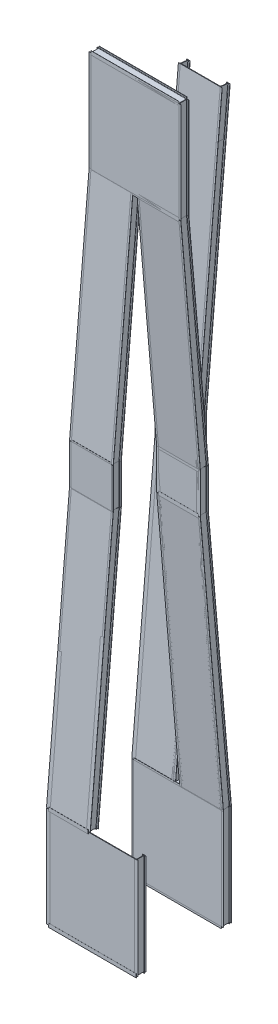
SolidWorks part; units mm, degrees
ref_plane "Plano frontal" through (0, 0, 0) normal (0, 0, 1) x (1, 0, 0)
ref_plane "Plano superior" through (0, 0, 0) normal (0, 1, 0) x (1, 0, 0)
ref_plane "Plano direito" through (0, 0, 0) normal (1, 0, 0) x (0, 0, -1)
sketch3d "3DSketch1"
  line L0 (-19546.6177, 14667.4814, 38871.7002) -> (-19546.6177, -9107.5186, 38871.7002) construction
  line L2 (-19546.6177, -9107.5186, 38871.7002) -> (-19546.6177, -9107.5186, 40471.7002) construction
  line L3 (-19546.6177, -9107.5186, 40471.7002) -> (-19546.6177, 892.4814, 39606.8353)
  line L4 (-19546.6177, 892.4814, 39606.8353) -> (-19546.6177, 2392.4814, 39606.8353)
  line L5 (-19546.6177, 892.4814, 38871.7002) -> (-19546.6177, 892.4814, 39606.8353) construction
  line L6 (-19546.6177, 892.4814, 39606.8353) -> (-19546.6177, 2392.4814, 39606.8353) construction
  line L7 (-19546.6177, 2392.4814, 39606.8353) -> (-19546.6177, 2392.4814, 38871.7002) construction
  line L8 (-19546.6177, 2392.4814, 39606.8353) -> (-19546.6177, 10892.4814, 38871.7002)
  line L9 (-19546.6177, 892.4814, 39606.8353) -> (-19546.6177, -9107.5186, 39606.8353) construction
  line L10 (-19546.6177, -9107.5186, 39606.8353) -> (-18046.6177, -9107.5186, 39606.8353) construction
  line L11 (-18046.6177, -9107.5186, 39606.8353) -> (-18046.6177, 892.4814, 39606.8353) construction
  line L12 (-18046.6177, 892.4814, 39606.8353) -> (-19546.6177, 892.4814, 39606.8353) construction
  line L13 (-18046.6177, 892.4814, 39606.8353) -> (-18046.6177, 2392.4814, 39606.8353) construction
  line L14 (-18046.6177, 2392.4814, 39606.8353) -> (-19546.6177, 2392.4814, 39606.8353) construction
  line L15 (-18046.6177, -9107.5186, 39606.8353) -> (-18046.6177, -9107.5186, 40471.7002) construction
  line L16 (-18046.6177, -9107.5186, 40471.7002) -> (-19546.6177, -9107.5186, 40471.7002) construction
  line L17 (-18046.6177, -9107.5186, 40471.7002) -> (-18046.6177, 892.4814, 39606.8353)
  line L18 (-18046.6177, 892.4814, 39606.8353) -> (-18046.6177, 2392.4814, 39606.8353)
  line L19 (-19546.6177, 10892.4814, 38871.7002) -> (-18046.6177, 10892.4814, 38871.7002) construction
  line L20 (-18046.6177, 10892.4814, 38871.7002) -> (-18046.6177, 2392.4814, 38871.7002) construction
  line L21 (-18046.6177, 2392.4814, 38871.7002) -> (-19546.6177, 2392.4814, 38871.7002) construction
  line L22 (-18046.6177, 2392.4814, 38871.7002) -> (-18046.6177, 2392.4814, 39606.8353) construction
  line L23 (-18046.6177, 2392.4814, 39606.8353) -> (-18046.6177, 10892.4814, 38871.7002)
  line L24 (-18046.6177, 10892.4814, 38871.7002) -> (-19546.6177, 10892.4814, 38871.7002)
  line L25 (-19546.6177, 892.4814, 39606.8353) -> (-18046.6177, 892.4814, 39606.8353)
  line L26 (-19546.6177, 2392.4814, 39606.8353) -> (-18046.6177, 2392.4814, 39606.8353)
  line L27 (-19546.6177, -9107.5186, 40471.7002) -> (-18046.6177, -9107.5186, 40471.7002)
  line L28 (-18046.6177, 2392.4814, 38871.7002) -> (-18046.6177, -9107.5186, 38871.7002) construction
  line L29 (-18046.6177, -9107.5186, 38871.7002) -> (-19546.6177, -9107.5186, 38871.7002) construction
  line L30 (-18046.6177, -9107.5186, 39606.8353) -> (-18046.6177, -9107.5186, 38871.7002) construction
  line L31 (-19546.6177, 14667.4814, 38871.7002) -> (-18046.6177, 14667.4814, 38871.7002) construction
  line L32 (-18046.6177, 14667.4814, 38871.7002) -> (-18046.6177, 10892.4814, 38871.7002) construction
  line L33 (-18046.6177, 892.4814, 39606.8353) -> (-18046.6177, 892.4814, 38871.7002) construction
  line L34 (-18046.6177, -9107.5186, 40471.7002) -> (-17746.6177, -9107.5186, 40471.7002)
  line L35 (-17746.6177, -9107.5186, 40471.7002) -> (-17746.6177, 892.4814, 41336.5651)
  line L36 (-17746.6177, -9107.5186, 40471.7002) -> (-17746.6177, 892.4814, 40471.7002) construction
  line L37 (-17746.6177, 892.4814, 40471.7002) -> (-17746.6177, 892.4814, 41336.5651) construction
  line L38 (-17746.6177, 892.4814, 40471.7002) -> (-16246.6177, 892.4814, 40471.7002) construction
  line L39 (-16246.6177, 892.4814, 40471.7002) -> (-16246.6177, -9107.5186, 40471.7002) construction
  line L40 (-17746.6177, -9107.5186, 40471.7002) -> (-16246.6177, -9107.5186, 40471.7002)
  line L41 (-16246.6177, -9107.5186, 40471.7002) -> (-16246.6177, 892.4814, 41336.5651)
  line L42 (-16246.6177, 892.4814, 41336.5651) -> (-17746.6177, 892.4814, 41336.5651)
  line L43 (-16246.6177, 892.4814, 41336.5651) -> (-16246.6177, 892.4814, 40471.7002) construction
  line L44 (-16246.6177, 892.4814, 40471.7002) -> (-16246.6177, 2392.4814, 40471.7002) construction
  line L45 (-18046.6177, 892.4814, 39606.8353) -> (-18046.6177, 892.4814, 41336.5651) construction
  line L46 (-18046.6177, 892.4814, 41336.5651) -> (-17746.6177, 892.4814, 41336.5651) construction
  line L47 (-16246.6177, 2392.4814, 40471.7002) -> (-17746.6177, 2392.4814, 40471.7002) construction
  line L48 (-17746.6177, 2392.4814, 40471.7002) -> (-17746.6177, 892.4814, 40471.7002) construction
  line L49 (-18046.6177, 2392.4814, 39606.8353) -> (-18046.6177, 2392.4814, 40471.7002) construction
  line L50 (-17746.6177, 2392.4814, 40471.7002) -> (-18046.6177, 2392.4814, 40471.7002) construction
  line L51 (-16246.6177, 2392.4814, 40471.7002) -> (-16246.6177, 2392.4814, 41336.5651) construction
  line L52 (-17746.6177, 2392.4814, 40471.7002) -> (-17746.6177, 2392.4814, 41336.5651) construction
  line L53 (-17746.6177, 892.4814, 41336.5651) -> (-17746.6177, 2392.4814, 41336.5651)
  line L54 (-17746.6177, 2392.4814, 41336.5651) -> (-16246.6177, 2392.4814, 41336.5651)
  line L55 (-16246.6177, 2392.4814, 41336.5651) -> (-16246.6177, 892.4814, 41336.5651)
  line L56 (-16246.6177, 2392.4814, 40471.7002) -> (-16246.6177, 10892.4814, 40471.7002) construction
  line L57 (-16246.6177, 10892.4814, 40471.7002) -> (-17746.6177, 10892.4814, 40471.7002) construction
  line L58 (-17746.6177, 10892.4814, 40471.7002) -> (-17746.6177, 2392.4814, 40471.7002) construction
  line L59 (-16246.6177, 10892.4814, 40471.7002) -> (-16246.6177, 10892.4814, 42071.7002) construction
  line L60 (-16246.6177, 10892.4814, 42071.7002) -> (-17746.6177, 10892.4814, 42071.7002)
  line L61 (-17746.6177, 10892.4814, 42071.7002) -> (-17746.6177, 10892.4814, 40471.7002) construction
  line L62 (-17746.6177, 10892.4814, 40471.7002) -> (-17746.6177, 10892.4814, 38871.7002) construction
  line L63 (-17746.6177, 10892.4814, 38871.7002) -> (-16246.6177, 10892.4814, 38871.7002) construction
  line L64 (-16246.6177, 10892.4814, 38871.7002) -> (-16246.6177, 10892.4814, 40471.7002) construction
  line L65 (-17746.6177, 10892.4814, 38871.7002) -> (-18046.6177, 10892.4814, 38871.7002) construction
  line L66 (-16246.6177, 2392.4814, 41336.5651) -> (-16246.6177, 10892.4814, 42071.7002)
  line L67 (-17746.6177, 10892.4814, 42071.7002) -> (-17746.6177, 2392.4814, 41336.5651)
  line L68 (-18046.6177, 10892.4814, 42071.7002) -> (-18046.6177, -9107.5186, 42071.7002) construction
  line L69 (-17746.6177, 10892.4814, 42071.7002) -> (-18046.6177, 10892.4814, 42071.7002)
  line L70 (-18046.6177, 2392.4814, 40471.7002) -> (-18046.6177, 2392.4814, 41336.5651) construction
  line L71 (-18046.6177, 2392.4814, 41336.5651) -> (-17746.6177, 2392.4814, 41336.5651) construction
  line L72 (-18046.6177, 2392.4814, 41336.5651) -> (-18046.6177, 2392.4814, 42806.8353) construction
  line L73 (-18046.6177, 10892.4814, 42071.7002) -> (-18046.6177, 2392.4814, 42806.8353)
  line L74 (-18046.6177, 2392.4814, 42806.8353) -> (-18046.6177, 892.4814, 42806.8353)
  line L75 (-18046.6177, 892.4814, 42806.8353) -> (-18046.6177, -9107.5186, 43671.7002)
  line L76 (-18046.6177, -9107.5186, 40471.7002) -> (-18046.6177, -9107.5186, 42071.7002) construction
  line L77 (-18046.6177, 892.4814, 41336.5651) -> (-18046.6177, 892.4814, 42806.8353) construction
  line L78 (-18046.6177, -9107.5186, 43671.7002) -> (-18046.6177, -9107.5186, 42071.7002)
  line L79 (-19546.6177, -9107.5186, 40471.7002) -> (-19546.6177, -9107.5186, 42071.7002) construction
  line L80 (-19546.6177, -9107.5186, 42071.7002) -> (-18046.6177, -9107.5186, 42071.7002) construction
  line L81 (-19546.6177, -9107.5186, 42071.7002) -> (-19546.6177, 10892.4814, 42071.7002) construction
  line L82 (-18046.6177, 10892.4814, 42071.7002) -> (-19546.6177, 10892.4814, 42071.7002) construction
  line L83 (-18046.6177, 892.4814, 42806.8353) -> (-19546.6177, 892.4814, 42806.8353) construction
  line L84 (-19546.6177, 892.4814, 42806.8353) -> (-19546.6177, 2392.4814, 42806.8353) construction
  line L85 (-19546.6177, 2392.4814, 42806.8353) -> (-18046.6177, 2392.4814, 42806.8353) construction
  line L86 (-19546.6177, -9107.5186, 42071.7002) -> (-19546.6177, -9107.5186, 42806.8353) construction
  line L87 (-19546.6177, -9107.5186, 42806.8353) -> (-19546.6177, 892.4814, 42806.8353) construction
  line L88 (-19546.6177, -9107.5186, 42071.7002) -> (-19546.6177, -9107.5186, 43671.7002)
  line L89 (-19546.6177, -9107.5186, 43671.7002) -> (-18046.6177, -9107.5186, 43671.7002)
  line L90 (-19546.6177, -9107.5186, 43671.7002) -> (-19546.6177, 892.4814, 42806.8353)
  line L91 (-19546.6177, 892.4814, 42806.8353) -> (-19546.6177, 2392.4814, 42806.8353)
  line L92 (-19546.6177, 2392.4814, 42806.8353) -> (-19546.6177, 10892.4814, 42071.7002)
  line L93 (-19546.6177, 10892.4814, 42071.7002) -> (-18046.6177, 10892.4814, 42071.7002)
  line L94 (-19546.6177, 14667.4814, 42071.7002) -> (-19546.6177, 14667.4814, 38871.7002) construction
  line L95 (-19546.6177, 10892.4814, 42071.7002) -> (-16246.6177, 10892.4814, 42071.7002)
  line L96 (-19546.6177, 10892.4814, 42071.7002) -> (-19546.6177, 14667.4814, 42071.7002)
  line L97 (-19546.6177, 14667.4814, 42071.7002) -> (-16246.6177, 14667.4814, 42071.7002)
  line L98 (-16246.6177, 10892.4814, 42071.7002) -> (-16246.6177, 14667.4814, 42071.7002)
  line L99 (-18046.6177, 2392.4814, 42806.8353) -> (-19546.6177, 2392.4814, 42806.8353)
  line L100 (-18046.6177, 892.4814, 42806.8353) -> (-19546.6177, 892.4814, 42806.8353)
  line L101 (-19546.6177, 14667.4814, 42071.7002) -> (-19546.6177, 14667.4814, 38871.7002)
  line L102 (-16246.6177, 14667.4814, 42071.7002) -> (-16246.6177, 14667.4814, 38871.7002)
  line L103 (-18046.6177, 14667.4814, 38871.7002) -> (-16246.6177, 14667.4814, 38871.7002) construction
  line L104 (-18046.6177, -9107.5186, 42071.7002) -> (-18046.6177, -9107.5186, 38871.7002)
  line L105 (-19546.6177, -9107.5186, 42071.7002) -> (-19546.6177, -9107.5186, 38871.7002)
  line L106 (-18046.6177, -9107.5186, 38871.7002) -> (-16246.6177, -9107.5186, 38871.7002) construction
  line L107 (-16246.6177, -9107.5186, 40471.7002) -> (-16246.6177, -9107.5186, 38871.7002)
  line L108 (-18046.6177, 892.4814, 39606.8353) -> (-18046.6177, 892.4814, 38871.7002)
  line L109 (-18046.6177, 2392.4814, 39606.8353) -> (-18046.6177, 2392.4814, 38871.7002)
  line L110 (-19546.6177, 892.4814, 39606.8353) -> (-19546.6177, 892.4814, 38871.7002)
  line L111 (-19546.6177, 2392.4814, 39606.8353) -> (-19546.6177, 2392.4814, 38871.7002)
  line L112 (-18046.6177, 892.4814, 38871.7002) -> (-16246.6177, 892.4814, 38871.7002) construction
  line L113 (-18046.6177, 2392.4814, 38871.7002) -> (-16246.6177, 2392.4814, 38871.7002) construction
  line L114 (-16246.6177, 892.4814, 41336.5651) -> (-16246.6177, 892.4814, 38871.7002)
  line L115 (-16246.6177, 2392.4814, 41336.5651) -> (-16246.6177, 2392.4814, 38871.7002)
  line L116 (-17746.6177, 892.4814, 41336.5651) -> (-17746.6177, 892.4814, 38871.7002)
  line L117 (-17746.6177, 2392.4814, 41336.5651) -> (-17746.6177, 2392.4814, 38871.7002)
  line L118 (-18046.6177, 892.4814, 42806.8353) -> (-18046.6177, 892.4814, 38871.7002)
  line L119 (-18046.6177, 2392.4814, 42806.8353) -> (-18046.6177, 2392.4814, 38871.7002)
  line L120 (-19546.6177, 892.4814, 42806.8353) -> (-19546.6177, 892.4814, 38871.7002)
  line L121 (-19546.6177, 2392.4814, 42806.8353) -> (-19546.6177, 2392.4814, 38871.7002)
  line L122 (-18046.6177, 14667.4814, 38871.7002) -> (-18046.6177, 14667.4814, 42071.7002)
  line L123 (-19546.6177, -12882.5186, 40471.7002) -> (-19546.6177, -12882.5186, 43671.7002) construction
  line L124 (-16246.6177, 892.4814, 41336.5651) -> (-17746.6177, 892.4814, 41336.5651)
  line L125 (-16246.6177, 892.4814, 41336.5651) -> (-16246.6177, 2392.4814, 41336.5651)
  line L126 (-16246.6177, 2392.4814, 41336.5651) -> (-17746.6177, 2392.4814, 41336.5651)
  line L127 (-17746.6177, 892.4814, 41336.5651) -> (-17746.6177, 2392.4814, 41336.5651)
  line L128 (-16246.6177, 892.4814, 41336.5651) -> (-17746.6177, 892.4814, 41336.5651)
  line L129 (-16246.6177, 892.4814, 41336.5651) -> (-16246.6177, -9107.5186, 40471.7002)
  line L130 (-16246.6177, -9107.5186, 40471.7002) -> (-17746.6177, -9107.5186, 40471.7002)
  line L131 (-17746.6177, 892.4814, 41336.5651) -> (-17746.6177, -9107.5186, 40471.7002)
  line L132 (-19546.6177, 2392.4814, 42806.8353) -> (-18046.6177, 2392.4814, 42806.8353)
  line L133 (-19546.6177, 2392.4814, 42806.8353) -> (-19546.6177, 10892.4814, 42071.7002)
  line L134 (-19546.6177, 10892.4814, 42071.7002) -> (-18046.6177, 10892.4814, 42071.7002)
  line L135 (-18046.6177, 2392.4814, 42806.8353) -> (-18046.6177, 10892.4814, 42071.7002)
  line L136 (-19546.6177, 892.4814, 42806.8353) -> (-18046.6422, 892.4569, 42806.5528)
  line L137 (-19546.6177, 892.4814, 42806.8353) -> (-19546.5932, 2392.5058, 42807.1179)
  line L138 (-19546.5932, 2392.5058, 42807.1179) -> (-18046.6177, 2392.4814, 42806.8353)
  line L139 (-18046.6422, 892.4569, 42806.5528) -> (-18046.6177, 2392.4814, 42806.8353)
  line L140 (-19546.6177, -9107.5186, 43671.7002) -> (-18046.6422, -9107.5431, 43671.4176)
  line L141 (-19546.6177, -9107.5186, 43671.7002) -> (-19546.6177, 892.4814, 42806.8353)
  line L142 (-19546.6177, 892.4814, 42806.8353) -> (-18046.6422, 892.4569, 42806.5528)
  line L143 (-18046.6422, -9107.5431, 43671.4176) -> (-18046.6422, 892.4569, 42806.5528)
  line L144 (-19546.6177, -9107.5186, 40471.7002) -> (-18046.6177, -9107.5186, 40471.7002)
  line L145 (-19546.6177, -9107.5186, 40471.7002) -> (-19546.6177, 892.4814, 39606.8353)
  line L146 (-19546.6177, 892.4814, 39606.8353) -> (-18046.6177, 892.4814, 39606.8353)
  line L147 (-18046.6177, -9107.5186, 40471.7002) -> (-18046.6177, 892.4814, 39606.8353)
  line L148 (-19546.6177, 2392.4814, 39606.8353) -> (-18046.6177, 2392.4814, 39606.8353)
  line L149 (-19546.6177, 2392.4814, 39606.8353) -> (-19546.6177, 892.4814, 39606.8353)
  line L150 (-19546.6177, 892.4814, 39606.8353) -> (-18046.6177, 892.4814, 39606.8353)
  line L151 (-18046.6177, 2392.4814, 39606.8353) -> (-18046.6177, 892.4814, 39606.8353)
  line L152 (-19546.6177, 10892.4814, 38871.7002) -> (-18046.6177, 10892.4814, 38871.7002)
  line L153 (-19546.6177, 10892.4814, 38871.7002) -> (-19546.6177, 2392.4814, 39606.8353)
  line L154 (-19546.6177, 2392.4814, 39606.8353) -> (-18046.6177, 2392.4814, 39606.8353)
  line L155 (-18046.6177, 10892.4814, 38871.7002) -> (-18046.6177, 2392.4814, 39606.8353)
  line L156 (-19546.6177, -9107.5186, 40471.7002) -> (-16246.6177, -9107.5186, 40471.7002)
  line L157 (-19546.6177, -9107.5186, 40471.7002) -> (-19546.6177, -12882.5186, 40471.7002)
  line L158 (-19546.6177, -12882.5186, 40471.7002) -> (-16246.6177, -12882.5186, 40471.7002)
  line L159 (-16246.6177, -9107.5186, 40471.7002) -> (-16246.6177, -12882.5186, 40471.7002)
  line L160 (-19546.6177, -12882.5186, 43671.7002) -> (-19546.6177, -9107.5186, 43671.7002) construction
  line L161 (-18046.6177, 10892.4814, 38871.7002) -> (-18046.6177, 13532.0913, 38871.7002) construction
  line L162 (-19546.6177, -9107.5186, 43671.7002) -> (-16246.6177, -9107.5186, 43671.7002)
  line L163 (-19546.6177, -9107.5186, 43671.7002) -> (-19546.6177, -12882.5186, 43671.7002)
  line L164 (-19546.6177, -12882.5186, 43671.7002) -> (-16246.6177, -12882.5186, 43671.7002)
  line L165 (-16246.6177, -9107.5186, 43671.7002) -> (-16246.6177, -12882.5186, 43671.7002)
  line L166 (-18046.6177, 10892.4814, 38871.7002) -> (-19546.6177, 10892.4814, 38871.7002)
  line L167 (-18046.6177, 10892.4814, 38871.7002) -> (-18046.6177, 12626.8564, 38721.7002)
  line L168 (-18046.6177, 12626.8564, 38721.7002) -> (-19546.6177, 12626.8564, 38721.7002)
  line L169 (-19546.6177, 10892.4814, 38871.7002) -> (-19546.6177, 12626.8564, 38721.7002)
  line L170 (-18046.6177, 12626.8564, 38871.7002) -> (-18046.6177, 12626.8564, 38721.7002) construction
  line L172 (-19546.6177, -9082.5186, 41771.7002) -> (-19546.6177, -9082.5186, 38871.7002) construction
  dimension "D1" = 10000
  dimension "D3" = 8500
  dimension "D2" = 1600
  dimension "D6" = 300
  dimension "D4" = 1500
  dimension "D5" = 1500
  dimension "D7" = 150
  dimension "D8" = 25
other "Al i beam standard AL I BEAM STD 12X17.3(1)"
ref_plane "Plane1" through (-18046.6177, 2392.4814, 39606.8353) normal (0, 0.9963, -0.0862) x (1, 0, 0)
sketch "Sketch1" plane through (-18046.6177, 2392.4814, 39606.8353) normal (0, 0.9963, -0.0862) x (1, 0, 0)
  line L0 (-69.596, -151.2794) -> (-69.596, -149.8037)
  line L1 (-63.2891, -142.7374) -> (-21.3386, -137.9576)
  line L2 (-8.7249, -123.825) -> (-8.7249, 123.825)
  line L3 (-20.6103, 137.8554) -> (-63.6533, 145.0298)
  line L4 (-69.596, 152.045) -> (-69.596, 153.5206)
  line L5 (-69.596, 153.5206) -> (69.596, 153.5206)
  line L6 (69.596, 153.5206) -> (69.596, 152.045)
  line L7 (63.6533, 145.0298) -> (20.6103, 137.8554)
  line L8 (8.7249, 123.825) -> (8.7249, -123.825)
  line L9 (21.3386, -137.9576) -> (63.2891, -142.7374)
  line L10 (69.596, -149.8037) -> (69.596, -151.2794)
  line L11 (69.596, -151.2794) -> (-69.596, -151.2794)
  line L14 (-8.7249, 0) -> (8.7249, 0) construction
  arc A0 (-21.3386, -137.9576) -> (-8.7249, -123.825) centre (-22.9489, -123.825) ccw
  arc A1 (-8.7249, 123.825) -> (-20.6103, 137.8554) centre (-22.9489, 123.825) ccw
  arc A2 (20.6103, 137.8554) -> (8.7249, 123.825) centre (22.9489, 123.825) ccw
  arc A3 (8.7249, -123.825) -> (21.3386, -137.9576) centre (22.9489, -123.825) ccw
  arc A4 (63.6533, 145.0298) -> (69.596, 152.045) centre (62.484, 152.045) ccw
  arc A5 (-63.6533, 145.0298) -> (-69.596, 152.045) centre (-62.484, 152.045) cw
  arc A6 (63.2891, -142.7374) -> (69.596, -149.8037) centre (62.484, -149.8037) cw
  arc A7 (-63.2891, -142.7374) -> (-69.596, -149.8037) centre (-62.484, -149.8037) ccw
  point P30 (0, 153.5206)
  point P31 (0, -151.2794)
  point P33 (0, 0)
  point P34 (0, 0)
  dimension "D7" = 6.5
  dimension "RI" = 14.224
  dimension "RA" = 7.112
  dimension "BF" = 139.192
  dimension "D6" = 9.463
  dimension "DEPTH" = 304.8
  dimension "TW" = 17.4498
  dimension "D1" = 247.65
other "Al i beam standard AL I BEAM STD 12X17.3(2)"
ref_plane "Plane2" through (-18046.6177, 892.4814, 39606.8353) normal (0, 1, 0) x (1, 0, 0)
sketch "Sketch11" plane through (-18046.6177, 892.4814, 39606.8353) normal (0, 1, 0) x (1, 0, 0)
  line L0 (-69.596, -151.2794) -> (-69.596, -149.8037)
  line L1 (-63.2891, -142.7374) -> (-21.3386, -137.9576)
  line L2 (-8.7249, -123.825) -> (-8.7249, 123.825)
  line L3 (-20.6103, 137.8554) -> (-63.6533, 145.0298)
  line L4 (-69.596, 152.045) -> (-69.596, 153.5206)
  line L5 (-69.596, 153.5206) -> (69.596, 153.5206)
  line L6 (69.596, 153.5206) -> (69.596, 152.045)
  line L7 (63.6533, 145.0298) -> (20.6103, 137.8554)
  line L8 (8.7249, 123.825) -> (8.7249, -123.825)
  line L9 (21.3386, -137.9576) -> (63.2891, -142.7374)
  line L10 (69.596, -149.8037) -> (69.596, -151.2794)
  line L11 (69.596, -151.2794) -> (-69.596, -151.2794)
  line L14 (-8.7249, 0) -> (8.7249, 0) construction
  arc A0 (-21.3386, -137.9576) -> (-8.7249, -123.825) centre (-22.9489, -123.825) ccw
  arc A1 (-8.7249, 123.825) -> (-20.6103, 137.8554) centre (-22.9489, 123.825) ccw
  arc A2 (20.6103, 137.8554) -> (8.7249, 123.825) centre (22.9489, 123.825) ccw
  arc A3 (8.7249, -123.825) -> (21.3386, -137.9576) centre (22.9489, -123.825) ccw
  arc A4 (63.6533, 145.0298) -> (69.596, 152.045) centre (62.484, 152.045) ccw
  arc A5 (-63.6533, 145.0298) -> (-69.596, 152.045) centre (-62.484, 152.045) cw
  arc A6 (63.2891, -142.7374) -> (69.596, -149.8037) centre (62.484, -149.8037) cw
  arc A7 (-63.2891, -142.7374) -> (-69.596, -149.8037) centre (-62.484, -149.8037) ccw
  point P30 (0, 153.5206)
  point P31 (0, -151.2794)
  point P33 (0, 0)
  point P34 (0, 0)
  dimension "D7" = 6.5
  dimension "RI" = 14.224
  dimension "RA" = 7.112
  dimension "BF" = 139.192
  dimension "D6" = 9.463
  dimension "DEPTH" = 304.8
  dimension "TW" = 17.4498
  dimension "D1" = 247.65
other "Al i beam standard AL I BEAM STD 12X17.3(3)"
ref_plane "Plane3" through (-19546.6177, -9107.5186, 40471.7002) normal (1, 0, 0) x (0, 0, -1)
sketch "Sketch12" plane through (-19546.6177, -9107.5186, 40471.7002) normal (1, 0, 0) x (0, 0, -1)
  line L0 (151.2794, -69.596) -> (149.8037, -69.596)
  line L1 (142.7374, -63.2891) -> (137.9576, -21.3386)
  line L2 (123.825, -8.7249) -> (-123.825, -8.7249)
  line L3 (-137.8554, -20.6103) -> (-145.0298, -63.6533)
  line L4 (-152.045, -69.596) -> (-153.5206, -69.596)
  line L5 (-153.5206, -69.596) -> (-153.5206, 69.596)
  line L6 (-153.5206, 69.596) -> (-152.045, 69.596)
  line L7 (-145.0298, 63.6533) -> (-137.8554, 20.6103)
  line L8 (-123.825, 8.7249) -> (123.825, 8.7249)
  line L9 (137.9576, 21.3386) -> (142.7374, 63.2891)
  line L10 (149.8037, 69.596) -> (151.2794, 69.596)
  line L11 (151.2794, 69.596) -> (151.2794, -69.596)
  line L14 (0, -8.7249) -> (0, 8.7249) construction
  arc A0 (137.9576, -21.3386) -> (123.825, -8.7249) centre (123.825, -22.9489) ccw
  arc A1 (-123.825, -8.7249) -> (-137.8554, -20.6103) centre (-123.825, -22.9489) ccw
  arc A2 (-137.8554, 20.6103) -> (-123.825, 8.7249) centre (-123.825, 22.9489) ccw
  arc A3 (123.825, 8.7249) -> (137.9576, 21.3386) centre (123.825, 22.9489) ccw
  arc A4 (-145.0298, 63.6533) -> (-152.045, 69.596) centre (-152.045, 62.484) ccw
  arc A5 (-145.0298, -63.6533) -> (-152.045, -69.596) centre (-152.045, -62.484) cw
  arc A6 (142.7374, 63.2891) -> (149.8037, 69.596) centre (149.8037, 62.484) cw
  arc A7 (142.7374, -63.2891) -> (149.8037, -69.596) centre (149.8037, -62.484) ccw
  point P30 (-153.5206, 0)
  point P31 (151.2794, 0)
  point P33 (0, 0)
  point P34 (0, 0)
  dimension "D7" = 6.5
  dimension "RI" = 14.224
  dimension "RA" = 7.112
  dimension "BF" = 139.192
  dimension "D6" = 9.463
  dimension "DEPTH" = 304.8
  dimension "TW" = 17.4498
  dimension "D1" = 247.65
other "Al i beam standard AL I BEAM STD 12X17.3(12)"
ref_plane "Plane4" through (-16246.6177, -9107.5186, 40471.7002) normal (0, 0.9963, 0.0862) x (1, 0, 0)
sketch "Sketch13" plane through (-16246.6177, -9107.5186, 40471.7002) normal (0, 0.9963, 0.0862) x (1, 0, 0)
  line L0 (-69.596, -151.2794) -> (-69.596, -149.8037)
  line L1 (-63.2891, -142.7374) -> (-21.3386, -137.9576)
  line L2 (-8.7249, -123.825) -> (-8.7249, 123.825)
  line L3 (-20.6103, 137.8554) -> (-63.6533, 145.0298)
  line L4 (-69.596, 152.045) -> (-69.596, 153.5206)
  line L5 (-69.596, 153.5206) -> (69.596, 153.5206)
  line L6 (69.596, 153.5206) -> (69.596, 152.045)
  line L7 (63.6533, 145.0298) -> (20.6103, 137.8554)
  line L8 (8.7249, 123.825) -> (8.7249, -123.825)
  line L9 (21.3386, -137.9576) -> (63.2891, -142.7374)
  line L10 (69.596, -149.8037) -> (69.596, -151.2794)
  line L11 (69.596, -151.2794) -> (-69.596, -151.2794)
  line L14 (-8.7249, 0) -> (8.7249, 0) construction
  arc A0 (-21.3386, -137.9576) -> (-8.7249, -123.825) centre (-22.9489, -123.825) ccw
  arc A1 (-8.7249, 123.825) -> (-20.6103, 137.8554) centre (-22.9489, 123.825) ccw
  arc A2 (20.6103, 137.8554) -> (8.7249, 123.825) centre (22.9489, 123.825) ccw
  arc A3 (8.7249, -123.825) -> (21.3386, -137.9576) centre (22.9489, -123.825) ccw
  arc A4 (63.6533, 145.0298) -> (69.596, 152.045) centre (62.484, 152.045) ccw
  arc A5 (-63.6533, 145.0298) -> (-69.596, 152.045) centre (-62.484, 152.045) cw
  arc A6 (63.2891, -142.7374) -> (69.596, -149.8037) centre (62.484, -149.8037) cw
  arc A7 (-63.2891, -142.7374) -> (-69.596, -149.8037) centre (-62.484, -149.8037) ccw
  point P30 (0, 153.5206)
  point P31 (0, -151.2794)
  point P33 (0, 0)
  point P34 (0, 0)
  dimension "D7" = 6.5
  dimension "RI" = 14.224
  dimension "RA" = 7.112
  dimension "BF" = 139.192
  dimension "D6" = 9.463
  dimension "DEPTH" = 304.8
  dimension "TW" = 17.4498
  dimension "D1" = 247.65
sketch "Sketch14" plane through (0, 3430.8218, 39668.877) normal (0, 0.0862, 0.9963) x (1, 0, 0)
  line L0 (-19477.0217, -2523.5543) -> (-19477.0217, -12560.8841) construction
  line L1 (-19477.0217, -2523.5543) -> (-18046.6177, -2523.5543)
  line L2 (-19477.0217, -2523.5543) -> (-19477.0217, -12504.7751)
  line L3 (-19477.0217, -12504.7751) -> (-18046.6177, -12504.7751)
  line L4 (-18046.6177, -2523.5543) -> (-18046.6177, -12504.7751)
  line L5 (-18046.6177, -12504.7751) -> (-19546.6177, -12504.7751) construction
  line L6 (-18046.6177, -12560.8841) -> (-18046.6177, -2523.5543) construction
  line L7 (-19546.6177, -2523.5543) -> (-18046.6177, -2523.5543) construction
extrude "Boss-Extrude5" add sketch "Sketch14" against normal blind 20 from surface at -129.2473 separate body starting at face at (-18046.6177, -4094.4837, 40189.9845)
sketch "Sketch15" plane through (0, 0, 40625.2208) normal (0, 0, 1) x (1, 0, 0)
  line L1 (-19546.6177, -9107.5186) -> (-16246.6177, -9107.5186)
  line L2 (-19546.6177, -9107.5186) -> (-19546.6177, -12882.5186)
  line L3 (-19546.6177, -12882.5186) -> (-16246.6177, -12882.5186)
  line L4 (-16246.6177, -9107.5186) -> (-16246.6177, -12882.5186)
extrude "Boss-Extrude6" add sketch "Sketch15" against normal blind 20 from surface at 0 separate body starting at face at (-18796.6177, -9107.5186, 40625.2208)
sketch "Sketch16" plane through (0, -3554.9206, 41103.769) normal (0, -0.0862, 0.9963) x (1, 0, 0)
  line L1 (-17746.6177, 4450.9204) -> (-16246.6177, 4450.9204)
  line L2 (-17746.6177, 4450.9204) -> (-17746.6177, -5573.1814)
  line L3 (-17746.6177, -5573.1814) -> (-16246.6177, -5573.1814)
  line L4 (-16246.6177, 4450.9204) -> (-16246.6177, -5573.1814)
extrude "Boss-Extrude7" add sketch "Sketch16" against normal blind 20 from surface at 0 separate body starting at face at (-16246.6177, -4120.5536, 41054.8494)
sketch "Sketch17" plane through (0, 0, 43822.9795) normal (0, 0, 1) x (1, 0, 0)
  line L1 (-19546.6177, -9107.5186) -> (-16246.6177, -9107.5186)
  line L2 (-19546.6177, -9107.5186) -> (-19546.6177, -12882.5186)
  line L3 (-19546.6177, -12882.5186) -> (-16246.6177, -12882.5186)
  line L4 (-16246.6177, -9107.5186) -> (-16246.6177, -12882.5186)
extrude "Boss-Extrude8" add sketch "Sketch17" against normal blind 20 from surface at 0 separate body starting at face at (-19546.6177, -10995.0186, 43822.9795)
sketch "Sketch18" plane through (0, 3694.3872, 42716.3524) normal (0, 0.0862, 0.9963) x (1, 0, 0)
  line L1 (-18046.6177, -12836.6116) -> (-19546.6177, -12836.6116)
  line L2 (-18046.6177, -12836.6116) -> (-18046.6177, -2799.2817)
  line L3 (-18046.6177, -2799.2817) -> (-19546.6177, -2799.2817)
  line L4 (-19546.6177, -12836.6116) -> (-19546.6177, -2799.2817)
extrude "Boss-Extrude9" add sketch "Sketch18" against normal blind 20 from surface at 0 separate body starting at face at (-19546.6177, -4094.4837, 43389.9845)
sketch "Sketch19" plane through (0, 0, 42960.356) normal (0, 0, 1) x (1, 0, 0)
  line L1 (-19555.3426, 2403.1507) -> (-18046.6177, 2403.1507)
  line L2 (-19555.3426, 2403.1507) -> (-19555.3426, 892.4814)
  line L3 (-19555.3426, 892.4814) -> (-18046.6177, 892.4814)
  line L4 (-18046.6177, 2403.1507) -> (-18046.6177, 892.4814)
extrude "Boss-Extrude10" add sketch "Sketch19" against normal blind 20 from surface at 0 separate body starting at face at (-18796.6177, 2392.4814, 42960.356)
sketch "Sketch20" plane through (0, 3705.5238, 42845.119) normal (0, 0.0862, 0.9963) x (1, 0, 0)
  line L1 (-18046.6177, -1306.8902) -> (-19546.6177, -1306.8902)
  line L2 (-18046.6177, -1306.8902) -> (-18046.6177, 7226.87)
  line L3 (-18046.6177, 7226.87) -> (-19546.6177, 7226.87)
  line L4 (-19546.6177, -1306.8902) -> (-19546.6177, 7226.87)
extrude "Boss-Extrude11" add sketch "Sketch20" against normal blind 20 from surface at 0 separate body starting at face at (-19546.6177, 6655.5163, 42589.9845)
sketch "Sketch21" plane through (0, 0, 42225.2208) normal (0, 0, 1) x (1, 0, 0)
  line L1 (-19546.6177, 14667.4814) -> (-16237.8928, 14667.4814)
  line L2 (-19546.6177, 14667.4814) -> (-19546.6177, 10881.812)
  line L3 (-19546.6177, 10881.812) -> (-16237.8928, 10881.812)
  line L4 (-16237.8928, 14667.4814) -> (-16237.8928, 10881.812)
extrude "Boss-Extrude12" add sketch "Sketch21" against normal blind 20 from surface at 0 separate body starting at face at (-17896.6177, 14667.4814, 42225.2208)
sketch "Sketch22" plane through (0, -3543.784, 40975.0024) normal (0, -0.0862, 0.9963) x (1, 0, 0)
  line L1 (-17746.6177, 14477.0722) -> (-16246.6177, 14477.0722)
  line L2 (-17746.6177, 14477.0722) -> (-17746.6177, 5945.3417)
  line L3 (-17746.6177, 5945.3417) -> (-16246.6177, 5945.3417)
  line L4 (-16246.6177, 14477.0722) -> (-16246.6177, 5945.3417)
extrude "Boss-Extrude13" add sketch "Sketch22" against normal blind 20 from surface at 0 separate body starting at face at (-16246.6177, 6629.4464, 41854.8494)
sketch "Sketch23" plane through (0, 0, 41487.8444) normal (0, 0, 1) x (1, 0, 0)
  line L1 (-17746.6177, 2392.4814) -> (-16246.6177, 2392.4814)
  line L2 (-17746.6177, 2392.4814) -> (-17746.6177, 892.4814)
  line L3 (-17746.6177, 892.4814) -> (-16246.6177, 892.4814)
  line L4 (-16246.6177, 2392.4814) -> (-16246.6177, 892.4814)
extrude "Boss-Extrude14" add sketch "Sketch23" against normal blind 20 from surface at 0 separate body starting at face at (-16246.6177, 1642.4814, 41487.8444)
sketch "Sketch24" plane through (0, 0, 39758.1147) normal (0, 0, 1) x (1, 0, 0)
  line L1 (-19546.6177, 2392.4814) -> (-18046.6177, 2392.4814)
  line L2 (-19546.6177, 2392.4814) -> (-19546.6177, 892.4814)
  line L3 (-19546.6177, 892.4814) -> (-18046.6177, 892.4814)
  line L4 (-18046.6177, 2392.4814) -> (-18046.6177, 892.4814)
extrude "Boss-Extrude15" add sketch "Sketch24" against normal blind 20 from surface at 0 separate body starting at face at (-19546.6177, 1642.4814, 39758.1147)
sketch "Sketch25" plane through (0, 3430.8218, 39668.877) normal (0, 0.0862, 0.9963) x (1, 0, 0)
  line L1 (-19546.6177, 9243.4469) -> (-18046.6177, 9243.4469)
  line L2 (-19546.6177, 9243.4469) -> (-19546.6177, -1029.1329)
  line L3 (-19546.6177, -1029.1329) -> (-18046.6177, -1029.1329)
  line L4 (-18046.6177, 9243.4469) -> (-18046.6177, -1029.1329)
extrude "Boss-Extrude16" add sketch "Sketch25" against normal blind 20 from surface at 0 separate body starting at face at (-19546.6177, 6655.5163, 39389.9845)
other "Al i beam standard AL I BEAM STD 12X17.3(21)"
ref_plane "Plane5" through (-18046.6177, 10892.4814, 38871.7002) normal (0, 0.9963, -0.0862) x (1, 0, 0)
sketch "Sketch110" plane through (-18046.6177, 10892.4814, 38871.7002) normal (0, 0.9963, -0.0862) x (1, 0, 0)
  line L0 (-69.596, -151.2794) -> (-69.596, -149.8037)
  line L1 (-63.2891, -142.7374) -> (-21.3386, -137.9576)
  line L2 (-8.7249, -123.825) -> (-8.7249, 123.825)
  line L3 (-20.6103, 137.8554) -> (-63.6533, 145.0298)
  line L4 (-69.596, 152.045) -> (-69.596, 153.5206)
  line L5 (-69.596, 153.5206) -> (69.596, 153.5206)
  line L6 (69.596, 153.5206) -> (69.596, 152.045)
  line L7 (63.6533, 145.0298) -> (20.6103, 137.8554)
  line L8 (8.7249, 123.825) -> (8.7249, -123.825)
  line L9 (21.3386, -137.9576) -> (63.2891, -142.7374)
  line L10 (69.596, -149.8037) -> (69.596, -151.2794)
  line L11 (69.596, -151.2794) -> (-69.596, -151.2794)
  line L14 (-8.7249, 0) -> (8.7249, 0) construction
  arc A0 (-21.3386, -137.9576) -> (-8.7249, -123.825) centre (-22.9489, -123.825) ccw
  arc A1 (-8.7249, 123.825) -> (-20.6103, 137.8554) centre (-22.9489, 123.825) ccw
  arc A2 (20.6103, 137.8554) -> (8.7249, 123.825) centre (22.9489, 123.825) ccw
  arc A3 (8.7249, -123.825) -> (21.3386, -137.9576) centre (22.9489, -123.825) ccw
  arc A4 (63.6533, 145.0298) -> (69.596, 152.045) centre (62.484, 152.045) ccw
  arc A5 (-63.6533, 145.0298) -> (-69.596, 152.045) centre (-62.484, 152.045) cw
  arc A6 (63.2891, -142.7374) -> (69.596, -149.8037) centre (62.484, -149.8037) cw
  arc A7 (-63.2891, -142.7374) -> (-69.596, -149.8037) centre (-62.484, -149.8037) ccw
  point P30 (0, 153.5206)
  point P31 (0, -151.2794)
  point P33 (0, 0)
  point P34 (0, 0)
  dimension "D7" = 6.5
  dimension "RI" = 14.224
  dimension "RA" = 7.112
  dimension "BF" = 139.192
  dimension "D6" = 9.463
  dimension "DEPTH" = 304.8
  dimension "TW" = 17.4498
  dimension "D1" = 247.65
